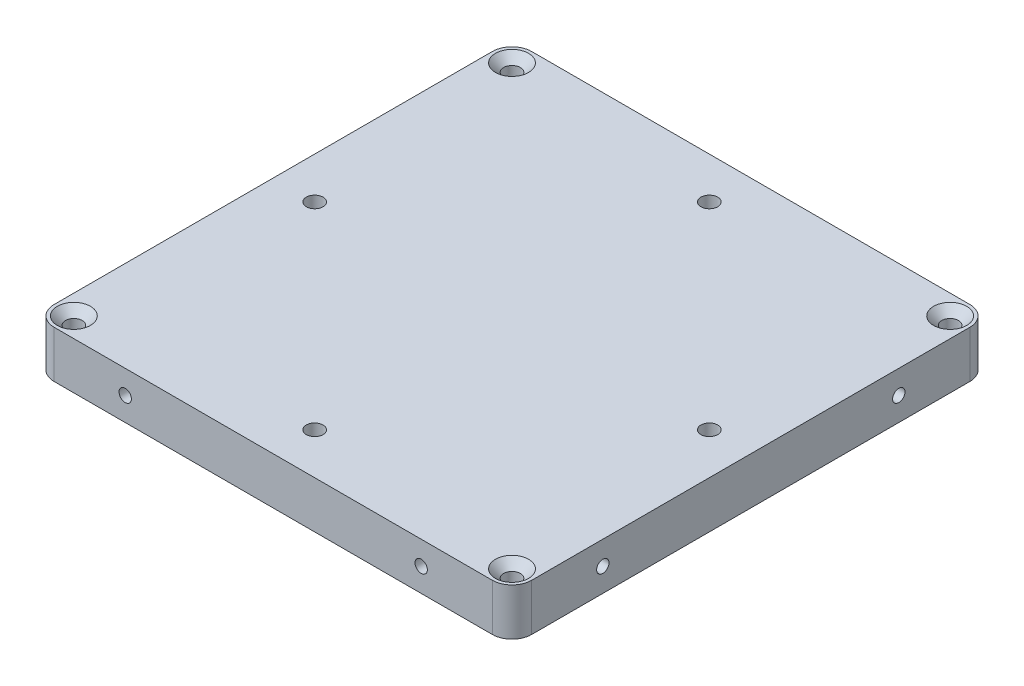
SolidWorks part; units mm, degrees
material "6061-T6 (SS)"
ref_plane "Front Plane" through (0, 0, 0) normal (0, 0, 1) x (1, 0, 0)
ref_plane "Top Plane" through (0, 0, 0) normal (0, 1, 0) x (1, 0, 0)
ref_plane "Right Plane" through (0, 0, 0) normal (1, 0, 0) x (0, 0, -1)
sketch "Sketch1" plane through (0, 0, 0) normal (0, 1, 0) x (1, 0, 0)
  line L1 (48.4125, -48.4125) -> (-48.4125, -48.4125)
  line L2 (48.4125, -48.4125) -> (48.4125, 48.4125)
  line L3 (48.4125, 48.4125) -> (-48.4125, 48.4125)
  line L4 (-48.4125, -48.4125) -> (-48.4125, 48.4125)
  line L5 (48.4125, -48.4125) -> (-48.4125, 48.4125) construction
  line L6 (48.4125, 48.4125) -> (-48.4125, -48.4125) construction
  point P0 (0, 0)
  dimension "D1" = 96.825
extrude "Boss-Extrude1" add sketch "Sketch1" along normal mid plane 9.525
fillet "Fillet1" radius 4 4 edges at (-48.4125, 0, -48.4125) (48.4125, 0, -48.4125) (48.4125, 0, 48.4125) (-48.4125, 0, 48.4125)
hole_wizard "CSK for M3 SFHCS2" positions "Sketch4" profile "Sketch3" countersink size "M3" standard "ANSI Metric" end condition through all
sketch "Sketch4" plane through (0, -4.7625, 0) normal (0, 1, 0) x (1, 0, 0)
  point P0 (-40, 0)
  point P2 (0, 40)
  point P4 (40, 0)
  point P6 (0, -40)
  dimension "D1" = 40
  dimension "D2" = 40
  dimension "D3" = 40
  dimension "D4" = 40
sketch "Sketch3" plane through (-40, -4.7625, 0) normal (1, 0, 0) x (0, 0, -1)
  line L0 (0, 0) -> (0, 9.525)
  line L1 (0, 9.525) -> (1.7, 9.525)
  line L2 (1.7, 9.525) -> (1.7, 1.66)
  line L3 (1.7, 1.66) -> (3.36, 0)
  line L5 (3.36, 0) -> (0, 0)
  line L6 (-1.7, 1.66) -> (-3.36, 0) construction
  line L11 (0, -6.35) -> (0, 107.95) construction
  dimension "Thru Hole Dia." = 3.4
  dimension "Thru Hole Depth" = 9.525
  dimension "Near C'Sink Dia." = 6.72
  dimension "Near C'Sink Angle" = 90
hole_wizard "CSK for M3 SFHCS1" positions "Sketch7" profile "Sketch6" countersink size "M3" standard "ANSI Metric"
sketch "Sketch7" plane through (0, 4.7625, 0) normal (0, 1, 0) x (1, 0, 0)
  arc A0 (-44.4125, 48.4125) -> (-48.4125, 44.4125) centre (-44.4125, 44.4125) ccw construction
  arc A1 (-48.4125, -44.4125) -> (-44.4125, -48.4125) centre (-44.4125, -44.4125) ccw construction
  arc A2 (48.4125, 44.4125) -> (44.4125, 48.4125) centre (44.4125, 44.4125) ccw construction
  arc A3 (44.4125, -48.4125) -> (48.4125, -44.4125) centre (44.4125, -44.4125) ccw construction
  point P0 (-44.4125, 44.4125)
  point P2 (44.4125, 44.4125)
  point P4 (44.4125, -44.4125)
  point P6 (-44.4125, -44.4125)
sketch "Sketch6" plane through (-44.4125, 4.7625, -44.4125) normal (1, 0, 0) x (0, 0, 1)
  line L0 (0, 0) -> (0, 36.0215)
  line L1 (0, 36.0215) -> (1.7, 35)
  line L2 (1.7, 35) -> (1.7, 1.66)
  line L3 (1.7, 1.66) -> (3.36, 0)
  line L5 (3.36, 0) -> (0, 0)
  line L6 (-1.7, 1.66) -> (-3.36, 0) construction
  line L10 (0, 36.0215) -> (-1.7, 35) construction
  line L11 (0, -6.35) -> (0, 107.95) construction
  dimension "Hole Dia." = 3.4
  dimension "Hole Depth" = 35
  dimension "Near C'Sink Dia." = 6.72
  dimension "Near C'Sink Angle" = 90
  dimension "Drill Angle" = 118
hole_wizard "M3x0.5 Tapped Hole1" positions "Sketch10" profile "Sketch11" tap size "M3x0.5" standard "ANSI Metric"
sketch "Sketch10" plane through (0, 0, 48.4125) normal (0, 0, 1) x (1, 0, 0)
  point P0 (-30, 0)
  point P2 (30, 0)
  dimension "D1" = 30
  dimension "D2" = 30
sketch "Sketch11" plane through (-30, 0, 48.4125) normal (1, 0, 0) x (0, -1, 0)
  line L0 (0, 0) -> (0, 10.7511)
  line L1 (0, 10.7511) -> (1.25, 10)
  line L2 (1.25, 10) -> (1.25, 0)
  line L5 (1.25, 0) -> (0, 0)
  line L10 (0, 10.7511) -> (-1.25, 10) construction
  line L11 (0, -6.35) -> (0, 107.95) construction
  dimension "Tap Drill Dia." = 2.5
  dimension "Tap Drill Depth" = 10
  dimension "Drill Angle" = 118
hole_wizard "M3x0.5 Tapped Hole2" positions "Sketch14" profile "Sketch13" tap size "M3x0.5" standard "ANSI Metric"
sketch "Sketch14" plane through (-48.4125, 0, 0) normal (-1, 0, 0) x (0, 0, 1)
  point P0 (-30, 0)
  point P2 (30, 0)
  dimension "D1" = 30
  dimension "D2" = 30
sketch "Sketch13" plane through (-48.4125, 0, -30) normal (0, 1, 0) x (0, 0, 1)
  line L0 (0, 0) -> (0, 10.7511)
  line L1 (0, 10.7511) -> (1.25, 10)
  line L2 (1.25, 10) -> (1.25, 0)
  line L5 (1.25, 0) -> (0, 0)
  line L10 (0, 10.7511) -> (-1.25, 10) construction
  line L11 (0, -6.35) -> (0, 107.95) construction
  dimension "Tap Drill Dia." = 2.5
  dimension "Tap Drill Depth" = 10
  dimension "Drill Angle" = 118
hole_wizard "M3x0.5 Tapped Hole3" positions "Sketch17" profile "Sketch16" tap size "M3x0.5" standard "ANSI Metric"
sketch "Sketch17" plane through (0, 0, -48.4125) normal (0, 0, -1) x (-1, 0, 0)
  point P0 (-30, 0)
  point P2 (30, 0)
  dimension "D1" = 30
  dimension "D2" = 30
sketch "Sketch16" plane through (30, 0, -48.4125) normal (1, 0, 0) x (0, 1, 0)
  line L0 (0, 0) -> (0, 10.7511)
  line L1 (0, 10.7511) -> (1.25, 10)
  line L2 (1.25, 10) -> (1.25, 0)
  line L5 (1.25, 0) -> (0, 0)
  line L10 (0, 10.7511) -> (-1.25, 10) construction
  line L11 (0, -6.35) -> (0, 107.95) construction
  dimension "Tap Drill Dia." = 2.5
  dimension "Tap Drill Depth" = 10
  dimension "Drill Angle" = 118
hole_wizard "M3x0.5 Tapped Hole4" positions "Sketch20" profile "Sketch19" tap size "M3x0.5" standard "ANSI Metric"
sketch "Sketch20" plane through (48.4125, 0, 0) normal (1, 0, 0) x (0, 0, -1)
  point P0 (-30, 0)
  point P2 (30, 0)
  dimension "D1" = 30
  dimension "D2" = 30
sketch "Sketch19" plane through (48.4125, 0, 30) normal (0, 1, 0) x (0, 0, -1)
  line L0 (0, 0) -> (0, 10.7511)
  line L1 (0, 10.7511) -> (1.25, 10)
  line L2 (1.25, 10) -> (1.25, 0)
  line L5 (1.25, 0) -> (0, 0)
  line L10 (0, 10.7511) -> (-1.25, 10) construction
  line L11 (0, -6.35) -> (0, 107.95) construction
  dimension "Tap Drill Dia." = 2.5
  dimension "Tap Drill Depth" = 10
  dimension "Drill Angle" = 118
